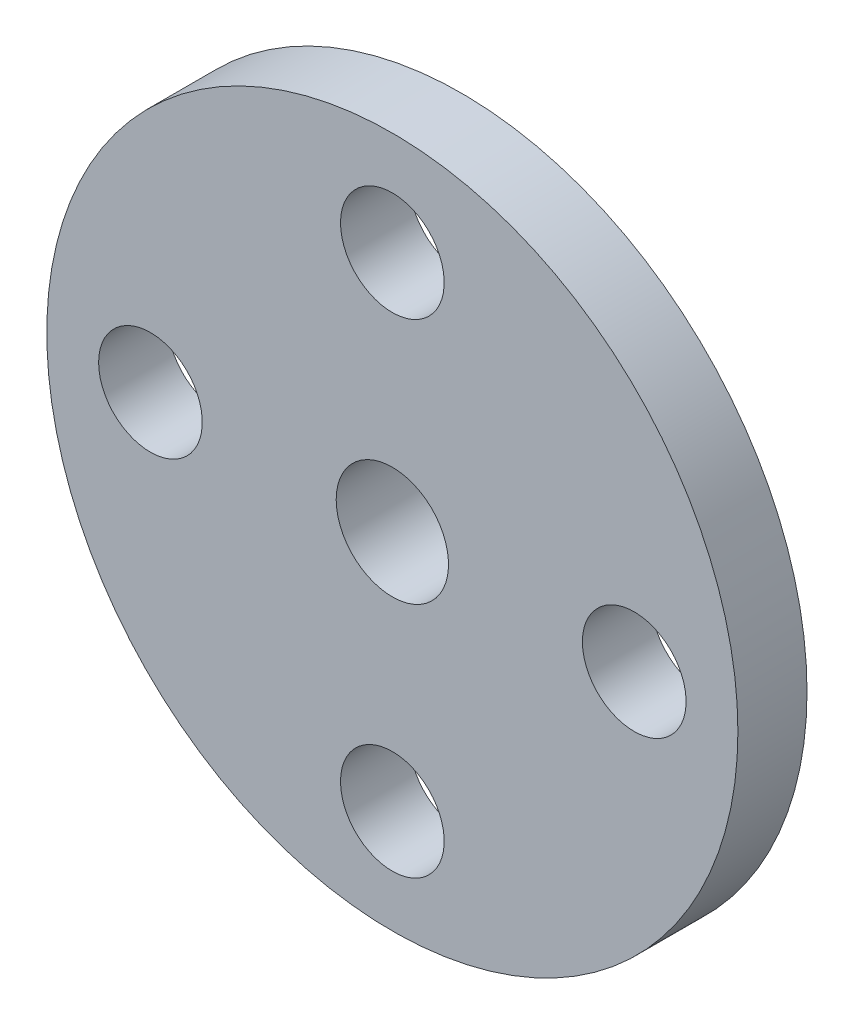
SolidWorks part; units mm, degrees
other "<Millerighe>-<Taglio-Estrusione2>"
ref_plane "Piano frontale" through (0, 0, 0) normal (0, 0, 1) x (1, 0, 0)
ref_plane "Piano superiore" through (0, 0, 0) normal (0, 1, 0) x (1, 0, 0)
ref_plane "Piano destro" through (0, 0, 0) normal (1, 0, 0) x (0, 0, -1)
sketch "Schizzo14" plane through (0, 0, 0) normal (0, 0, 1) x (1, 0, 0)
  line L0 (0, 10) -> (0, -10) construction
  line L1 (0, -10) -> (-10, 0) construction
  line L2 (-10, 0) -> (10, 0) construction
  circle A0 centre (0, 0) radius 10
  dimension "D1" = 20
extrude "Estrusione-Estrusione2" add sketch "Schizzo14" along normal blind 2
hole_wizard "Foro Ø3.0 (3)-1" positions "Schizzo3D14" profile "Schizzo18" hole size "Ø3.0" standard "ISO" end condition through all
sketch3d "Schizzo3D14"
  point P0 (7, 0, 0)
  point P2 (-7, 0, 0)
  point P4 (0, -7, 0)
  point P6 (0, 7, 0)
  dimension "D1" = 7
  dimension "D2" = 7
  dimension "D3" = 7
  dimension "D4" = 7
sketch "Schizzo18" plane through (7, 0, 0) normal (1, 0, 0) x (0, 1, 0)
  line L0 (0, 0) -> (0, 2)
  line L1 (0, 2) -> (1.5, 2)
  line L2 (1.5, 2) -> (1.5, 0)
  line L5 (1.5, 0) -> (0, 0)
  line L11 (0, -6.35) -> (0, 107.95) construction
  dimension "Thru Hole Dia." = 3
  dimension "Thru Hole Depth" = 2
cosmetic thread "Filettatura cosmetica2" parameters "D1"=1.9999, "D2"=3
cosmetic thread "Filettatura cosmetica3" parameters "D1"=1.9999, "D2"=3
cosmetic thread "Filettatura cosmetica4" parameters "D1"=1.9999, "D2"=3
cosmetic thread "Filettatura cosmetica5" parameters "D1"=1.9999, "D2"=3
sketch "Schizzo19" plane through (0, 0, 0) normal (0, 0, 1) x (1, 0, 0)
  circle A0 centre (0, 0) radius 4.5
  dimension "D1" = 9
extrude "Estrusione-Estrusione3" add sketch "Schizzo19" against normal blind 2
sketch "Schizzo20" plane through (0, 0, -2) normal (0, 0, -1) x (-1, 0, 0)
  circle A0 centre (0, 0) radius 1.625
  dimension "D1" = 3.25
extrude "Taglio-Estrusione1" cut sketch "Schizzo20" against normal through all
